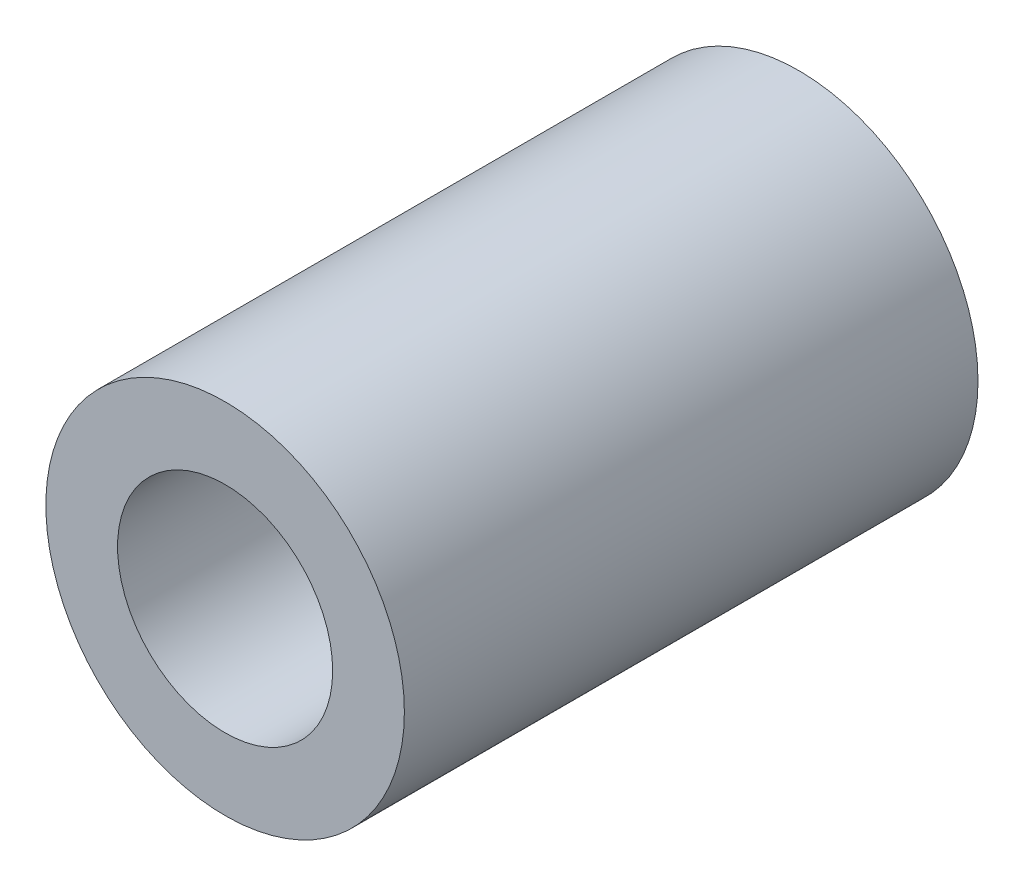
SolidWorks part; units mm, degrees
material "ﾎﾟﾘｵｷｼﾒﾁﾚﾝ(POM)ｱｾﾀｰﾙ共重合体"
ref_plane "Front Plane" through (0, 0, 0) normal (0, 0, 1) x (1, 0, 0)
ref_plane "Top Plane" through (0, 0, 0) normal (0, 1, 0) x (1, 0, 0)
ref_plane "Right Plane" through (0, 0, 0) normal (1, 0, 0) x (0, 0, -1)
sketch "Sketch2" plane through (0, 0, 0) normal (0, 0, 1) x (1, 0, 0)
  circle A0 centre (0, 0) radius 2.5
  circle A1 centre (0, 0) radius 1.5
  dimension "D1" = 3
  dimension "D2" = 5
  dimension "D3" = 5
extrude "Boss-Extrude1" add sketch "Sketch2" along normal blind 8
